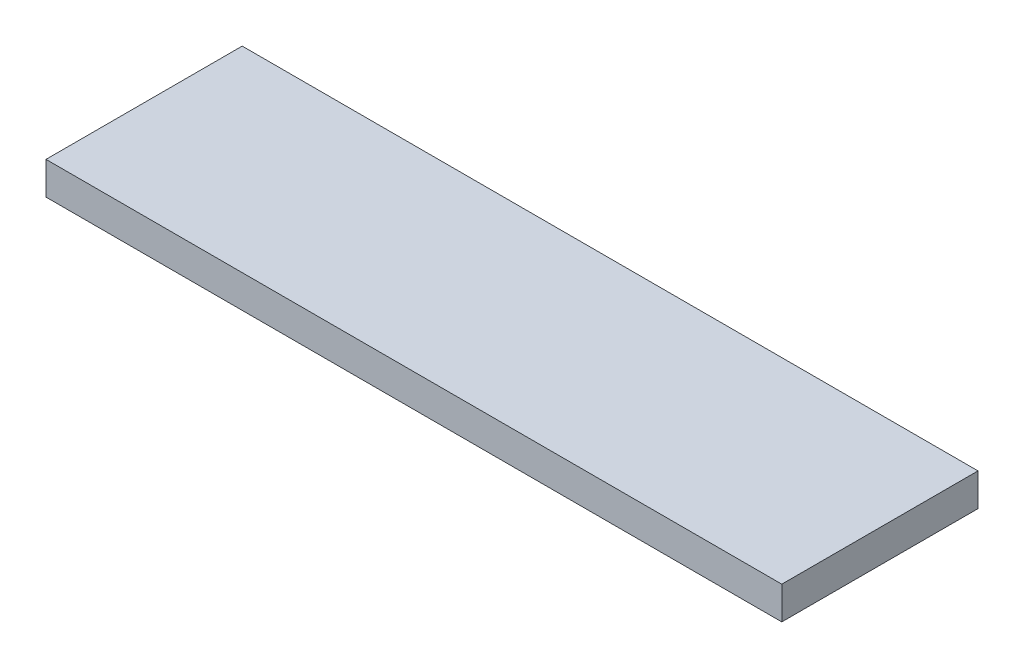
SolidWorks part; units mm, degrees
ref_plane "Front Plane" through (0, 0, 0) normal (0, 0, 1) x (1, 0, 0)
ref_plane "Top Plane" through (0, 0, 0) normal (0, 1, 0) x (1, 0, 0)
ref_plane "Right Plane" through (0, 0, 0) normal (1, 0, 0) x (0, 0, -1)
sketch "Sketch1" plane through (0, 0, 0) normal (0, 1, 0) x (1, 0, 0)
  line L1 (0, 0) -> (285.75, 0)
  line L2 (0, 0) -> (0, 76.2)
  line L3 (0, 76.2) -> (285.75, 76.2)
  line L4 (285.75, 0) -> (285.75, 76.2)
  dimension "D1" = 76.2
  dimension "D2" = 285.75
extrude "Boss-Extrude1" add sketch "Sketch1" along normal blind 12.7
